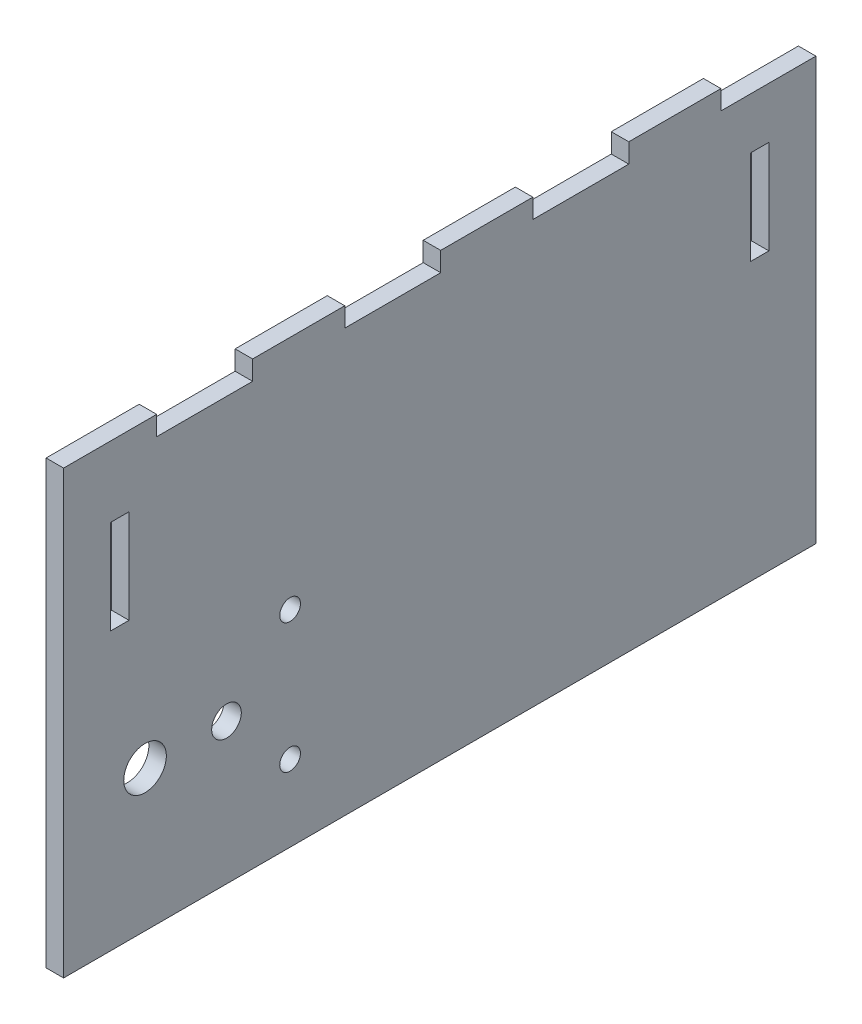
SolidWorks part; units mm, degrees
ref_plane "Front Plane" through (0, 0, 0) normal (0, 0, 1) x (1, 0, 0)
ref_plane "Top Plane" through (0, 0, 0) normal (0, 1, 0) x (1, 0, 0)
ref_plane "Right Plane" through (0, 0, 0) normal (1, 0, 0) x (0, 0, -1)
sketch "Sketch1" plane through (0, 0, 0) normal (1, 0, 0) x (0, 0, -1)
  line L0 (0, 0) -> (0, 59.6392)
  line L1 (0, 59.6392) -> (12.7, 59.6392)
  line L2 (12.7, 57.15) -> (25.4, 57.15)
  line L3 (25.4, 57.15) -> (25.4, 59.6392)
  line L4 (25.4, 59.6392) -> (38.1, 59.6392)
  line L5 (38.1, 59.6392) -> (38.1, 57.15)
  line L6 (38.1, 57.15) -> (50.8, 57.15)
  line L7 (50.8, 57.15) -> (50.8, 59.6392)
  line L8 (50.8, 59.6392) -> (63.5, 59.6392)
  line L9 (63.5, 59.6392) -> (63.5, 57.15)
  line L10 (63.5, 57.15) -> (76.2, 57.15)
  line L11 (76.2, 57.15) -> (76.2, 59.6392)
  line L12 (76.2, 59.6392) -> (88.9, 59.6392)
  line L13 (88.9, 59.6392) -> (88.9, 57.15)
  line L14 (88.9, 57.15) -> (101.6, 57.15)
  line L15 (101.6, 57.15) -> (101.6, 0)
  line L16 (101.6, 0) -> (0, 0)
  line L17 (12.7, 59.6392) -> (12.7, 57.15)
  dimension "D1" = 101.6
  dimension "D2" = 2.4892
  dimension "D10" = 57.15
extrude "Boss-Extrude1" add sketch "Sketch1" along normal blind 2.3622
sketch "Sketch2" plane through (2.3622, 0, 0) normal (1, 0, 0) x (0, 0, -1)
  line L0 (11, 19.05) -> (30.591, 19.05) construction
  line L1 (0, 59.6392) -> (0, 0) construction
  line L2 (50.8, 59.6392) -> (50.8, 0) construction
  line L3 (0, 0) -> (101.6, 0) construction
  line L4 (30.591, 27.8) -> (30.591, 10.3) construction
  circle A4 centre (30.591, 10.3) radius 1.4
  circle A5 centre (30.591, 27.8) radius 1.4
  circle A6 centre (22, 19.05) radius 2
  circle A7 centre (11, 19.05) radius 2.877
  dimension "D2" = 4
  dimension "D3" = 2.8
  dimension "D1" = 5.754
  dimension "D4" = 2.8
  dimension "D8" = 11
  dimension "D5" = 11
  dimension "D6" = 19.591
  dimension "D7" = 19.05
  dimension "D10" = 17.5
  dimension "D11" = 8.75
extrude "Cut-Extrude1" cut sketch "Sketch2" against normal up to next
sketch "Sketch3" plane through (2.3622, 0, 0) normal (1, 0, 0) x (0, 0, -1)
  line L0 (12.7, 59.6392) -> (12.7, 57.15)
  line L1 (50.8, 59.6392) -> (50.927, 59.6392)
  line L2 (12.7, 57.15) -> (25.4, 57.15)
  line L3 (25.4, 57.15) -> (25.4, 59.6392)
  line L4 (12.573, 59.6392) -> (12.573, 57.023)
  line L5 (12.573, 57.023) -> (25.527, 57.023)
  line L6 (25.527, 57.023) -> (25.527, 59.6392)
  line L7 (12.7, 59.6392) -> (12.573, 59.6392)
  line L8 (12.573, 59.6392) -> (12.5023, 60.3412)
  line L9 (25.4, 59.6392) -> (25.527, 59.6392)
  line L10 (38.1, 59.6392) -> (38.1, 57.15)
  line L11 (38.1, 57.15) -> (50.8, 57.15)
  line L12 (50.8, 57.15) -> (50.8, 59.6392)
  line L13 (37.973, 59.6392) -> (37.973, 57.023)
  line L14 (37.973, 57.023) -> (50.927, 57.023)
  line L15 (50.927, 57.023) -> (50.927, 59.6392)
  line L16 (63.5, 59.6392) -> (63.5, 57.15)
  line L17 (63.5, 57.15) -> (76.2, 57.15)
  line L18 (76.2, 57.15) -> (76.2, 59.6392)
  line L19 (63.373, 59.6392) -> (63.373, 57.023)
  line L20 (63.373, 57.023) -> (76.327, 57.023)
  line L21 (76.327, 57.023) -> (76.327, 59.6392)
  line L22 (37.973, 59.6392) -> (38.1, 59.6392)
  line L23 (63.373, 59.6392) -> (63.5, 59.6392)
  line L24 (76.2, 59.6392) -> (76.327, 59.6392)
  line L25 (88.9, 59.6392) -> (88.9, 57.15)
  line L26 (88.9, 57.15) -> (101.6, 57.15)
  line L27 (88.773, 59.6392) -> (88.773, 57.023)
  line L28 (88.773, 57.023) -> (101.6, 57.023)
  line L29 (88.773, 59.6392) -> (88.9, 59.6392)
  line L30 (101.6, 57.15) -> (101.6, 57.023)
  line M6 (101.6, 0) -> (101.6, 57.15)
  line M7 (101.6, 57.15) -> (88.9, 57.15)
  line M8 (88.9, 57.15) -> (88.9, 59.6392)
  line M9 (88.9, 59.6392) -> (76.2, 59.6392)
  line M10 (76.2, 59.6392) -> (76.2, 57.15)
  line M11 (76.2, 57.15) -> (63.5, 57.15)
  line M12 (63.5, 57.15) -> (63.5, 59.6392)
  line M13 (63.5, 59.6392) -> (50.8, 59.6392)
  line M14 (50.8, 59.6392) -> (50.8, 57.15)
  line M15 (50.8, 57.15) -> (38.1, 57.15)
  line M16 (38.1, 57.15) -> (38.1, 59.6392)
  line M17 (38.1, 59.6392) -> (25.4, 59.6392)
  line M18 (25.4, 59.6392) -> (25.4, 57.15)
  line M19 (25.4, 57.15) -> (12.7, 57.15)
  line M20 (12.7, 57.15) -> (12.7, 59.6392)
  line M21 (12.7, 59.6392) -> (0, 59.6392)
  dimension "D1" = 0.127
  dimension "D2" = 0.127
  dimension "D3" = 0.127
  dimension "D4" = 0.127
extrude "Cut-Extrude2" cut sketch "Sketch3" against normal through all contours L5 L6 L4 M17 M18 M19 M20 M21 | L14 L15 L13 M13 M14 M15 M16 M17 | L20 L21 L19 M9 M10 M11 M12 M13 | L27 L28 M6 M7 M8 M9
sketch "Sketch4" plane through (2.3622, 0, 0) normal (1, 0, 0) x (0, 0, -1)
  line L0 (0, 59.6392) -> (0, 0) construction
  line L1 (6.35, 50.1142) -> (8.8392, 50.1142)
  line L2 (6.35, 50.1142) -> (6.35, 37.4142)
  line L3 (6.35, 37.4142) -> (8.8392, 37.4142)
  line L4 (8.8392, 50.1142) -> (8.8392, 37.4142)
  line L5 (12.573, 59.6392) -> (0, 59.6392) construction
  line L6 (50.8, 0) -> (50.8, 53.7349) construction
  line L7 (0, 0) -> (101.6, 0) construction
  line L8 (92.7608, 50.1142) -> (92.7608, 37.4142)
  line L9 (95.25, 37.4142) -> (92.7608, 37.4142)
  line L10 (95.25, 50.1142) -> (95.25, 37.4142)
  line L11 (95.25, 50.1142) -> (92.7608, 50.1142)
  dimension "D1" = 2.4892
  dimension "D2" = 12.7
  dimension "D3" = 6.35
  dimension "D4" = 9.525
extrude "Cut-Extrude3" cut sketch "Sketch4" against normal through all
